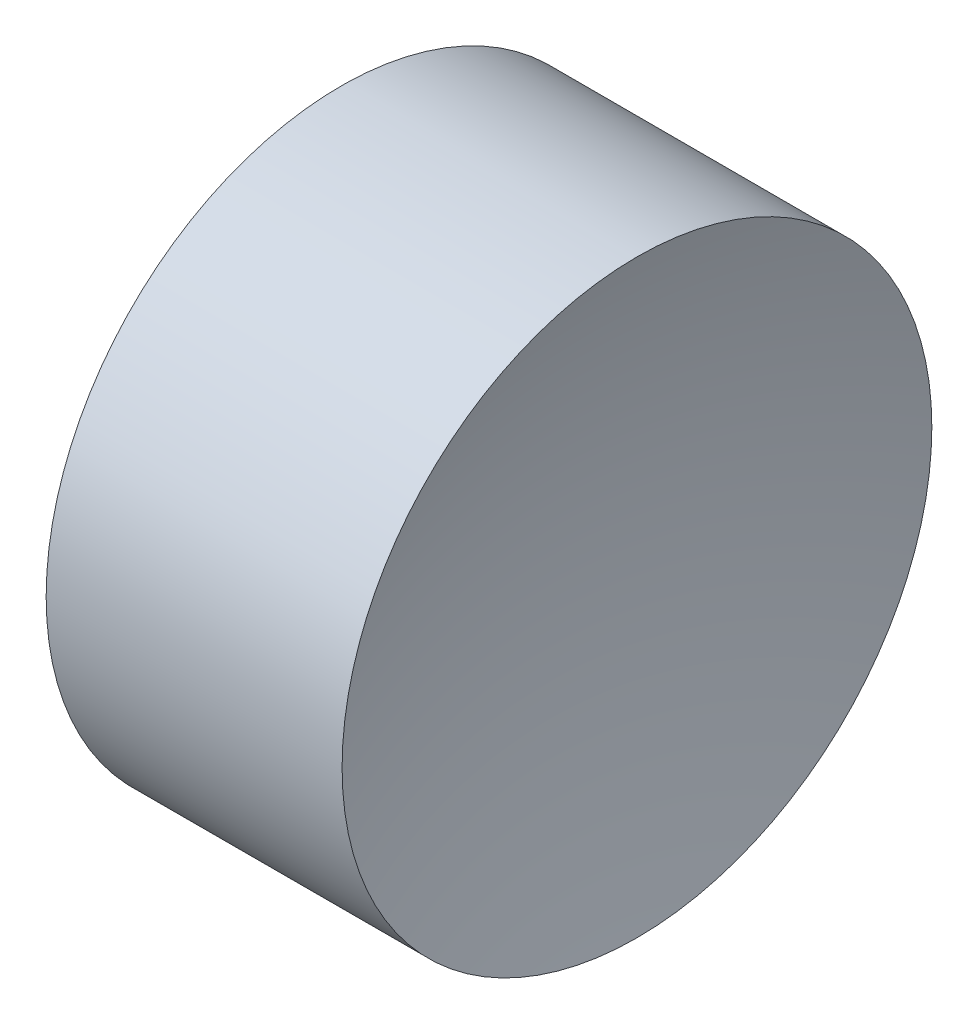
SolidWorks part; units mm, degrees
ref_plane "前视基准面" through (0, 0, 0) normal (0, 0, 1) x (1, 0, 0)
ref_plane "上视基准面" through (0, 0, 0) normal (0, 1, 0) x (1, 0, 0)
ref_plane "右视基准面" through (0, 0, 0) normal (1, 0, 0) x (0, 0, -1)
sketch "草图1" plane through (0, 0, 0) normal (0, 0, 1) x (1, 0, 0)
  line L0 (10.5782, 6.5156) -> (13.4181, 6.5156) construction
  line L1 (11.0806, 6.5156) -> (11.0806, 8.5156)
  line L2 (11.0806, 8.5156) -> (13.0877, 8.5156)
  line L3 (12.7906, 6.5156) -> (11.0806, 6.5156)
  arc A0 (13.0877, 8.5156) -> (12.7906, 6.5156) centre (19.6706, 6.5156) ccw
revolve "旋转1" add sketch "草图1" angle 360 about L0
